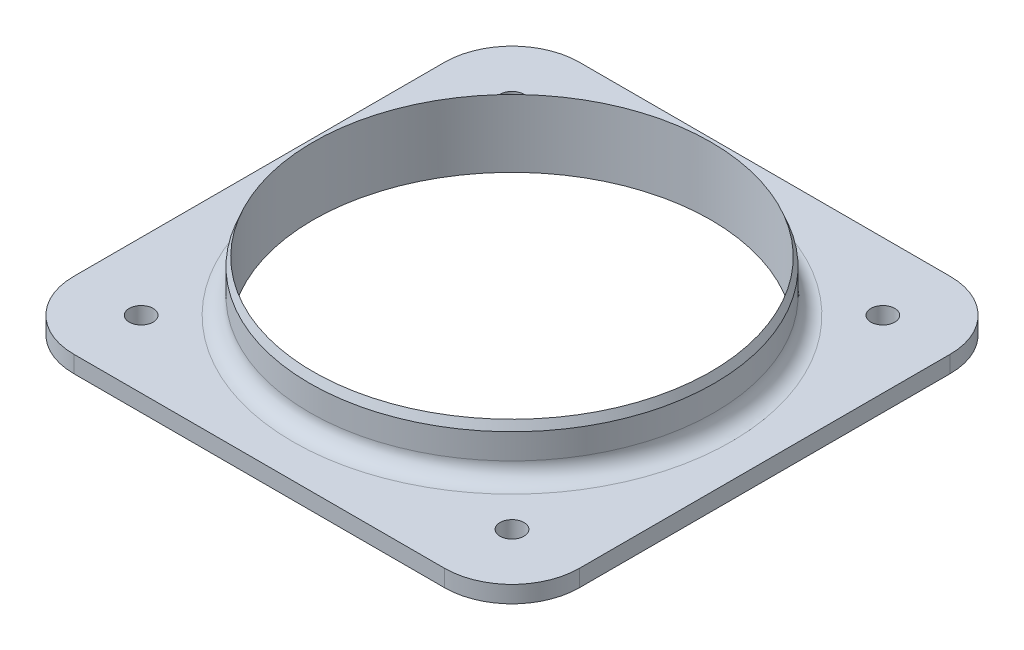
SolidWorks part; units mm, degrees
material "ABS"
ref_plane "Front Plane" through (0, 0, 0) normal (0, 0, 1) x (1, 0, 0)
ref_plane "Top Plane" through (0, 0, 0) normal (0, 1, 0) x (1, 0, 0)
ref_plane "Right Plane" through (0, 0, 0) normal (1, 0, 0) x (0, 0, -1)
sketch "Sketch1" plane through (0, 0, 0) normal (0, 1, 0) x (1, 0, 0)
  line L1 (47.625, -47.625) -> (-47.625, -47.625)
  line L2 (47.625, -47.625) -> (47.625, 47.625)
  line L3 (47.625, 47.625) -> (-47.625, 47.625)
  line L4 (-47.625, -47.625) -> (-47.625, 47.625)
  line L5 (47.625, -47.625) -> (-47.625, 47.625) construction
  line L6 (47.625, 47.625) -> (-47.625, -47.625) construction
  circle A0 centre (0, 0) radius 37.465
  point P0 (0, 0)
  dimension "D1" = 74.93
  dimension "D3" = 95.25
extrude "Boss-Extrude1" add sketch "Sketch1" along normal blind 3.175
sketch "Sketch2" plane through (0, 3.175, 0) normal (0, 1, 0) x (1, 0, 0)
  line L1 (34.925, -34.925) -> (-34.925, -34.925) construction
  line L2 (34.925, -34.925) -> (34.925, 34.925) construction
  line L3 (34.925, 34.925) -> (-34.925, 34.925) construction
  line L4 (-34.925, -34.925) -> (-34.925, 34.925) construction
  line L5 (34.925, -34.925) -> (-34.925, 34.925) construction
  line L6 (34.925, 34.925) -> (-34.925, -34.925) construction
  circle A0 centre (-34.925, 34.925) radius 2.25
  point P0 (0, 0)
  dimension "D2" = 4.5
  dimension "D1" = 69.85
extrude "Cut-Extrude1" cut sketch "Sketch2" against normal through all
pattern_circular "CirPattern1" count 4 over 360 about axis through (0, 0, 0) along (0, 1, 0) of "Cut-Extrude1"
fillet "Fillet1" radius 12.7 4 edges at (-47.625, 1.5875, -47.625) (-47.625, 1.5875, 47.625) (47.625, 1.5875, 47.625) (47.625, 1.5875, -47.625)
sketch "Sketch4" plane through (0, 0, 0) normal (0, 0, 1) x (1, 0, 0)
  line L0 (-34.925, 3.175) -> (34.925, 3.175) construction
  line L1 (37.465, 3.175) -> (38.1, 3.175)
  line L2 (37.465, 3.175) -> (37.465, 9.525)
  line L3 (0, 0) -> (0, 34.8088) construction
  line L4 (37.465, 12.7) -> (38.1, 11.1125)
  line L5 (37.465, 9.525) -> (37.465, 12.7)
  line L6 (38.1, 11.1125) -> (38.1, 10.3505)
  line L11 (38.1, 3.175) -> (38.1, 10.3505)
  point P15 (38.1, 7.9375)
  dimension "D1" = 6.35
  dimension "D2" = 37.465
  dimension "D3" = 0.635
  dimension "D4" = 1.5875
  dimension "D5" = 4.7625
  dimension "D6" = 3.175
revolve "Revolve1" add sketch "Sketch4" angle 360 about L3
fillet "Fillet2" radius 3.175 1 edges at (0, 3.175, 38.1)
